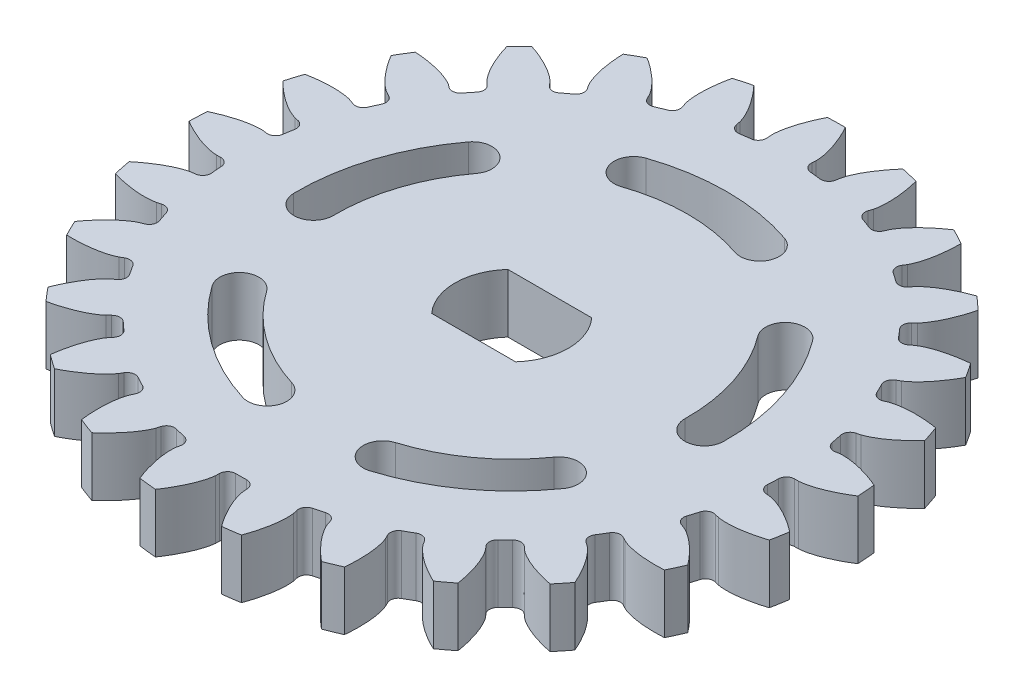
SolidWorks part; units mm, degrees
ref_plane "Front Plane" through (0, 0, 0) normal (0, 0, 1) x (1, 0, 0)
ref_plane "Top Plane" through (0, 0, 0) normal (0, 1, 0) x (1, 0, 0)
ref_plane "Right Plane" through (0, 0, 0) normal (1, 0, 0) x (0, 0, -1)
sketch "Sketch1" plane through (0, 0, 0) normal (0, 1, 0) x (1, 0, 0)
  circle A0 centre (0, 0) radius 16.875
  dimension "D1" = 33.75
extrude "Boss-Extrude1" add sketch "Sketch1" against normal blind 3
sketch "Sketch2" plane through (0, 0, 0) normal (0, 1, 0) x (1, 0, 0)
  line L0 (14.4732, 0) -> (14.6827, 0)
  line L1 (15.6233, 0.2329) -> (0, 0) construction
  line L2 (0, 0) -> (17.8928, -0.8582) construction
  line L3 (14.0464, -0.6737) -> (17.8928, -0.8582)
  line L4 (17.6949, 1.4689) -> (17.8928, -0.8582)
  circle A0 centre (0, 0) radius 14.6827 construction
  circle A1 centre (0, 0) radius 14.0625 construction
  circle A2 centre (0, 0) radius 15.625 construction
  circle A3 centre (0, 0) radius 16.875 construction
  arc A4 (14.0464, -0.6737) -> (14.0567, -0.4047) centre (0, 0) ccw
  arc A5 (14.4732, 0) -> (14.0567, -0.4047) centre (14.4732, -0.4167) ccw
  spline S0 degree 4 poles (14.6827, 0) (14.6877, 0.0001) (14.7018, 0.0005) (14.7284, 0.0022) (14.7717, 0.0062) (14.8268, 0.0131) (14.8979, 0.0242) (14.9813, 0.04) (15.0727, 0.0602) (15.1717, 0.0851) (15.2701, 0.1128) (15.3678, 0.1428) (15.4647, 0.1749) (15.5817, 0.2165) (15.7211, 0.27) (15.8829, 0.3379) (16.065, 0.4211) (16.2487, 0.5125) (16.4281, 0.6078) (16.6074, 0.7103) (16.7795, 0.8138) (16.9563, 0.9275) (17.1184, 1.0357) (17.2975, 1.1636) (17.4414, 1.2689) (17.6284, 1.4149) (17.7379, 1.5032) (17.8652, 1.6091) (17.9211, 1.6574) (17.9556, 1.6871) knots 0 0 0 0 0 0.005377 0.015084 0.028532 0.04661 0.064855 0.092111 0.119476 0.146842 0.174209 0.201575 0.228941 0.256307 0.307035 0.361767 0.4165 0.471232 0.525964 0.580697 0.635429 0.690161 0.744894 0.799626 0.854358 0.909091 0.954545 1 1 1 1 1 construction
  spline S1 degree 4 poles (14.6827, 0) (14.6877, 0.0001) (14.7018, 0.0005) (14.7284, 0.0022) (14.7717, 0.0062) (14.8268, 0.0131) (14.8979, 0.0242) (14.9813, 0.04) (15.0727, 0.0602) (15.1717, 0.0851) (15.2701, 0.1128) (15.3678, 0.1428) (15.4647, 0.1749) (15.5817, 0.2165) (15.7211, 0.27) (15.8829, 0.3379) (16.065, 0.4211) (16.2487, 0.5125) (16.4281, 0.6078) (16.6074, 0.7103) (16.7795, 0.8138) (16.9563, 0.9275) (17.1184, 1.0357) (17.2975, 1.1636) (17.4414, 1.2689) (17.5878, 1.3832) (17.6588, 1.4397) (17.6949, 1.4689) knots 0 0 0 0 0 0.005377 0.015084 0.028532 0.04661 0.064855 0.092111 0.119476 0.146842 0.174209 0.201575 0.228941 0.256307 0.307035 0.361767 0.4165 0.471232 0.525964 0.580697 0.635429 0.690161 0.744894 0.799626 0.854358 0.909091 0.909091 0.909091 0.909091 0.909091
  point P11 (17.8928, -0.8582)
  point P12 (15.6233, 0.2329)
  dimension "D1" = 29.3654
  dimension "D2" = 28.125
  dimension "D3" = 31.25
  dimension "D4" = 33.75
  dimension "D6" = 0.4167
  dimension "D5" = 3.6
extrude "Cut-Extrude1" cut sketch "Sketch2" against normal through all contours L3 L4 S1 L0 A5 A4
ref_plane "Plane2" through (0, 0, 0) normal (0.0479, 0, -0.9989) x (-0.9989, 0, -0.0479)
mirror "Mirror2" about plane through (0, 0, 0) normal (0.0479, 0, -0.9989) of "Cut-Extrude1"
pattern_circular "CirPattern19" count 25 over 360 about axis through (0, 0, 0) along (0, 1, 0) of "Mirror2", "Cut-Extrude1"
sketch "Sketch3" plane through (0, 0, 0) normal (0, 1, 0) x (1, 0, 0)
  line L0 (2.0125, 1.8) -> (-2.0125, 1.8) construction
  line L1 (-2.0125, -1.8) -> (2.0125, -1.8) construction
  line L2 (-2.1465, 1.95) -> (2.1465, 1.95)
  line L3 (-2.1465, -1.95) -> (2.1465, -1.95)
  arc A0 (2.0125, -1.8) -> (2.0125, 1.8) centre (0, 0) ccw construction
  arc A1 (2.1465, -1.95) -> (2.1465, 1.95) centre (0, 0) ccw
  arc A2 (-2.1465, 1.95) -> (-2.1465, -1.95) centre (0, 0) ccw
  arc A3 (-2.0125, 1.8) -> (-2.0125, -1.8) centre (0, 0) ccw construction
  dimension "D1" = 5.4
  dimension "D3" = 0.2
  dimension "D2" = 3.6
  dimension "D4" = 0.15
extrude "Cut-Extrude2" cut sketch "Sketch3" against normal through all
sketch "Sketch4" plane through (0, 0, 0) normal (0, 1, 0) x (1, 0, 0)
  line L0 (0, 0) -> (0, 10) construction
  line L1 (0, 0) -> (-4.7781, 6.5765) construction
  line L2 (0, 0) -> (4.7781, 6.5765) construction
  arc A0 (3.2244, 9.4659) -> (-3.2244, 9.4659) centre (0, 0) ccw construction
  arc A1 (3.5468, 10.4125) -> (-3.5468, 10.4125) centre (0, 0) ccw
  arc A2 (2.902, 8.5193) -> (-2.902, 8.5193) centre (0, 0) ccw
  arc A3 (2.902, 8.5193) -> (3.5468, 10.4125) centre (3.2244, 9.4659) ccw
  arc A4 (-3.5468, 10.4125) -> (-2.902, 8.5193) centre (-3.2244, 9.4659) ccw
  point P4 (0, 10)
  point P10 (4.171, 9.1435)
  dimension "D4" = 10
  dimension "D5" = 1
  dimension "D1" = 72
  dimension "D2" = 36
  dimension "D3" = 2
extrude "Cut-Extrude3" cut sketch "Sketch4" against normal through all
pattern_circular "CirPattern20" count 5 over 360 about axis through (0, 0, 0) along (0, 1, 0) of "Cut-Extrude3"
equation "\"m\"= 1.25'Module"
equation "\"phi\"= 20'Pressure angle"
equation "\"N\"= 25'Number of teeth"
equation "\"add\"= 1.00 * \"m\"'Addendum"
equation "\"ded\"= 1.25 * \"m\"'Dedendum"
equation "\"base_dia\"= \"dia\" * cos ( \"phi\" )'Base circle diameter"
equation "\"ded_dia\"= \"dia\" - 2 * \"ded\"'Dedendum circle diameter"
equation "\"dia\"= \"m\" * \"N\"'Pitch circle diameter"
equation "\"add_dia\"= \"dia\" + 2 * \"add\"'Addendum circle diameter"
equation "\"quarter_angle\"= 360 / ( 4 * \"N\" )"
equation "\"circ_pitch\"= pi * \"m\"'Circular pitch"
equation "\"clearance\"= \"ded\" - \"add\"'Clearance"
equation "\"fillet_radius\"= \"m\" / 3"
equation "\"D1@Sketch1\"=\"add_dia\""
equation "\"D1@Sketch2\"=\"base_dia\""
equation "\"D3@Sketch2\"=\"dia\""
equation "\"D4@Sketch2\"=\"add_dia\""
equation "\"D2@Sketch2\"=\"ded_dia\""
equation "\"D5@Sketch2\"=\"quarter_angle\""
equation "\"D1@CirPattern19\"=\"N\""
equation "\"D6@Sketch2\"=\"fillet_radius\""
